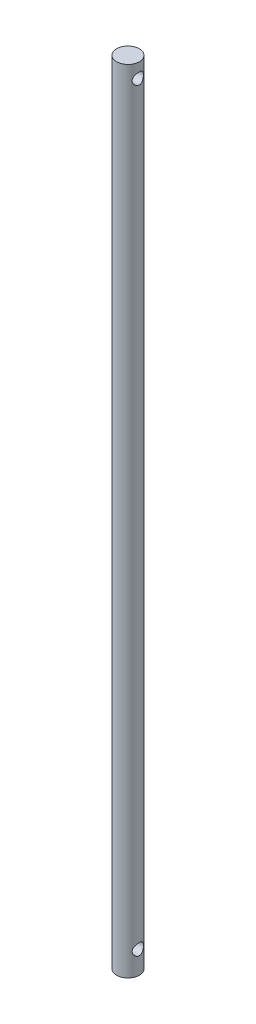
SolidWorks part; units mm, degrees
material "1060 Alloy"
ref_plane "Front Plane" through (0, 0, 0) normal (0, 0, 1) x (1, 0, 0)
ref_plane "Top Plane" through (0, 0, 0) normal (0, 1, 0) x (1, 0, 0)
ref_plane "Right Plane" through (0, 0, 0) normal (1, 0, 0) x (0, 0, -1)
sketch "Sketch1" plane through (0, 0, 0) normal (0, 1, 0) x (1, 0, 0)
  circle A0 centre (0, 0) radius 5
  circle A1 centre (0, 0) radius 4.5
extrude "Boss-Extrude1" add sketch "Sketch1" along normal blind 350
sketch "Sketch2" plane through (0, 350, 0) normal (0, 1, 0) x (1, 0, 0)
  circle A0 centre (0, 0) radius 5
  point P3 (0, 0)
extrude "Boss-Extrude2" add sketch "Sketch2" against normal blind 30
sketch "Sketch3" plane through (0, 0, 0) normal (0, -1, 0) x (-1, 0, 0)
  circle A0 centre (0, 0) radius 5
extrude "Boss-Extrude4" add sketch "Sketch3" against normal blind 30
sketch "Sketch4" plane through (0, 0, 0) normal (1, 0, 0) x (0, 0, -1)
  circle A0 centre (0, 10) radius 2.5
  dimension "D1" = 10
extrude "Cut-Extrude1" cut sketch "Sketch4" against normal mid plane 30
sketch "Sketch5" plane through (0, 0, 0) normal (1, 0, 0) x (0, 0, -1)
  circle A0 centre (0, 343.6043) radius 2.5
extrude "Cut-Extrude2" cut sketch "Sketch5" against normal mid plane 30
